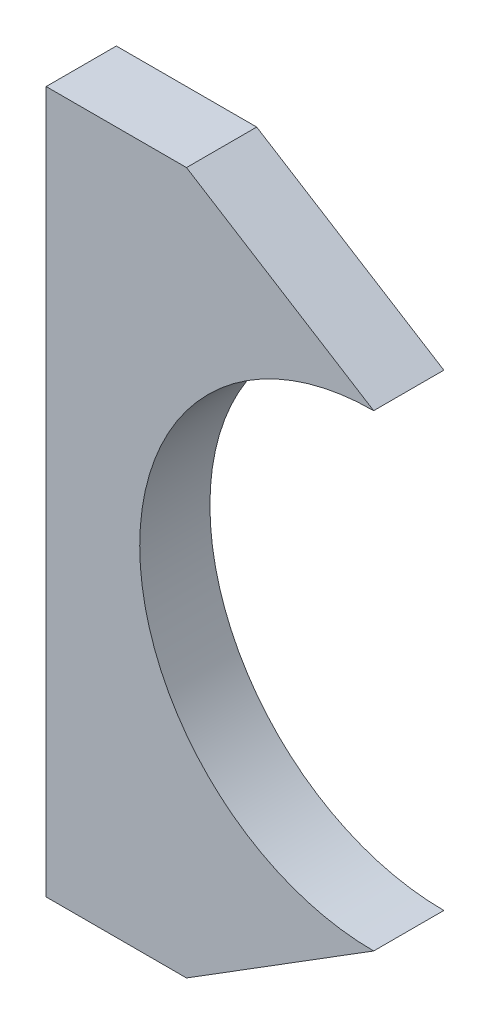
SolidWorks part; units mm, degrees
ref_plane "Front Plane" through (0, 0, 0) normal (0, 0, 1) x (1, 0, 0)
ref_plane "Top Plane" through (0, 0, 0) normal (0, 1, 0) x (1, 0, 0)
ref_plane "Right Plane" through (0, 0, 0) normal (1, 0, 0) x (0, 0, -1)
sketch "Sketch1" plane through (0, 0, 0) normal (0, 0, 1) x (1, 0, 0)
  line L0 (0, 50) -> (-40, 75)
  line L1 (-40, 75) -> (-70, 75)
  line L2 (-70, 75) -> (-70, -75)
  line L3 (-70, -75) -> (-40, -75)
  line L4 (-40, -75) -> (0, -50)
  line L7 (0, -8.25) -> (0, 8.25) construction
  line L8 (8.25, 0) -> (-8.25, 0) construction
  arc A0 (0, 50) -> (0, -50) centre (0, 0) ccw
  dimension "D1" = 100
  dimension "D2" = 150
  dimension "D3" = 75
  dimension "D4" = 70
  dimension "D5" = 30
  dimension "D6" = 30
extrude "Boss-Extrude1" add sketch "Sketch1" along normal mid plane 15
